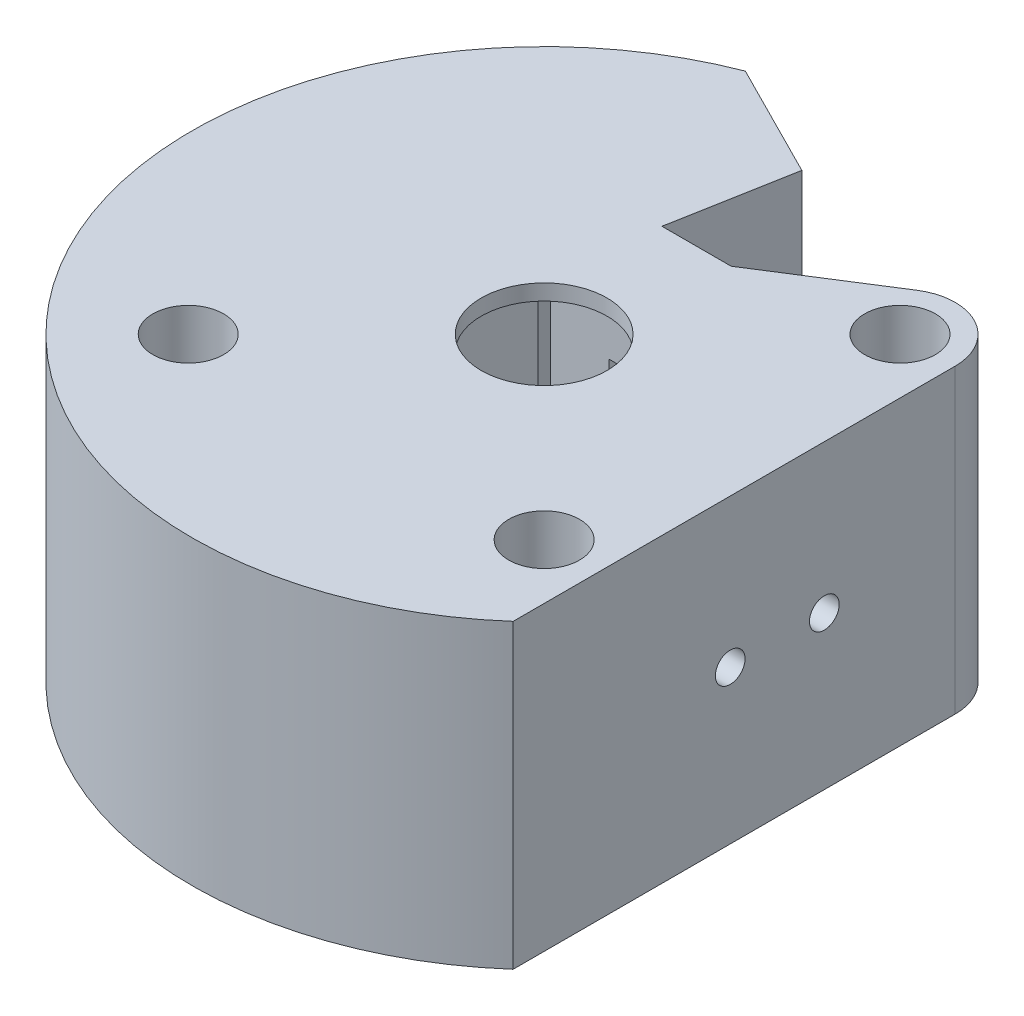
SolidWorks part; units mm, degrees
ref_plane "Front Plane" through (0, 0, 0) normal (0, 0, 1) x (1, 0, 0)
ref_plane "Top Plane" through (0, 0, 0) normal (0, 1, 0) x (1, 0, 0)
ref_plane "Right Plane" through (0, 0, 0) normal (1, 0, 0) x (0, 0, -1)
sketch "Sketch2" plane through (0, 0, 0) normal (0, 1, 0) x (1, 0, 0)
  line L0 (-46.3406, 15.0473) -> (-20.9548, -39.0545) construction
  line L1 (-17.9605, 17.9605) -> (-3.0236, 17.9605) construction
  line L2 (-17.9605, 17.9605) -> (-17.9605, -17.9605) construction
  line L3 (-17.9605, -17.9605) -> (17.9605, -17.9605) construction
  line L4 (17.9605, 17.9605) -> (17.9605, -17.9605) construction
  line L5 (-17.9605, 17.9605) -> (17.9605, -17.9605) construction
  line L6 (-17.9605, -17.9605) -> (17.9605, 17.9605) construction
  line L7 (10.05, -30.05) -> (-10.05, -30.05)
  line L8 (10.05, -30.05) -> (10.05, 10.05)
  line L9 (10.05, 10.05) -> (3.4925, 10.05)
  line L10 (-10.05, -30.05) -> (-10.05, 10.05)
  line L11 (10.05, -30.05) -> (-10.05, 10.05) construction
  line L12 (10.05, 10.05) -> (-10.05, -30.05) construction
  line L13 (-3.4925, 15.384) -> (3.4925, 15.384) construction
  line L14 (-3.4925, 15.384) -> (-3.4925, 10.05)
  line L15 (0, 10.05) -> (3.4925, 10.05) construction
  line L16 (3.4925, 15.384) -> (3.4925, 10.05)
  line L17 (0, 12.717) -> (3.4925, 10.05) construction
  line L18 (0, 12.717) -> (3.4925, 15.384) construction
  line L19 (-1.3182, 27.3309) -> (-10.8398, 32.142)
  line L20 (-1.3182, 27.3309) -> (-23.3118, -16.1961) construction
  line L21 (-23.3118, -16.1961) -> (-32.8333, -11.3851) construction
  line L22 (-10.8398, 32.142) -> (-32.8333, -11.3851) construction
  line L23 (-1.3182, 27.3309) -> (-32.8333, -11.3851) construction
  line L24 (-23.3118, -16.1961) -> (-10.8398, 32.142) construction
  line L25 (23.5324, -17.9605) -> (23.5324, -26.6597)
  line L26 (23.5324, -17.9605) -> (23.5324, 17.9605)
  line L27 (3.4925, 15.384) -> (14.9767, 22.6661)
  line L28 (-10.8398, 32.142) -> (-12.8493, 33.1573)
  line L29 (-3.4925, 15.384) -> (-1.3182, 27.3309)
  line L30 (-3.0236, 17.9605) -> (7.5558, 17.9605) construction
  line L31 (7.5558, 17.9605) -> (17.9605, 17.9605) construction
  line L32 (-3.4925, 15.384) -> (0, 12.717) construction
  line L33 (-3.4925, 10.05) -> (0, 12.717) construction
  line L34 (0, 10.05) -> (-3.4925, 10.05) construction
  line L35 (-3.4925, 10.05) -> (-10.05, 10.05)
  line L36 (-3.4925, 10.05) -> (0, 10.05) construction
  line L37 (3.4925, 10.05) -> (0, 10.05) construction
  arc A0 (-12.8493, 33.1573) -> (23.5324, -26.6597) centre (0, 0) ccw
  circle A1 centre (-17.9605, 17.9605) radius 3.5719 construction
  circle A2 centre (17.9605, 17.9605) radius 3.5719
  circle A3 centre (17.9605, -17.9605) radius 3.5719
  circle A4 centre (-17.9605, -17.9605) radius 3.5719
  arc A5 (-4.4901, 4.4901) -> (4.4901, 4.4901) centre (0, 0) ccw construction
  arc A6 (-7.1064, 7.1064) -> (7.1064, 7.1064) centre (0, 0) ccw construction
  circle A7 centre (-17.9605, -17.9605) radius 5.5719 construction
  arc A8 (23.5324, -17.9605) -> (17.9605, -12.3886) centre (17.9605, -17.9605) ccw construction
  arc A9 (23.5324, 17.9605) -> (14.9767, 22.6661) centre (17.9605, 17.9605) ccw
  arc A10 (23.5324, -26.6597) -> (-12.8493, 33.1573) centre (0, 0) ccw construction
  arc A11 (0, 10.05) -> (-7.1064, 7.1064) centre (0, 0) ccw construction
  arc A12 (4.4901, 4.4901) -> (-4.4901, 4.4901) centre (0, 0) ccw construction
  arc A13 (7.1064, 7.1064) -> (0, 10.05) centre (0, 0) ccw construction
  arc A14 (14.0206, 14.0206) -> (17.9605, 12.3886) centre (17.9605, 17.9605) ccw construction
  arc A15 (12.3886, 17.9605) -> (14.0206, 14.0206) centre (17.9605, 17.9605) ccw construction
  arc A16 (14.9767, 22.6661) -> (12.3886, 17.9605) centre (17.9605, 17.9605) ccw construction
  arc A17 (17.9605, 12.3886) -> (23.5324, 17.9605) centre (17.9605, 17.9605) ccw construction
  arc A18 (12.3886, -17.9605) -> (23.5324, -17.9605) centre (17.9605, -17.9605) ccw construction
  arc A19 (14.0206, -14.0206) -> (12.3886, -17.9605) centre (17.9605, -17.9605) ccw construction
  arc A20 (17.9605, -12.3886) -> (14.0206, -14.0206) centre (17.9605, -17.9605) ccw construction
  point P12 (0, -10)
  point P17 (0, 12.717)
  point P23 (-17.0758, 7.9729)
  point P35 (-32.1922, -15.1054)
  dimension "D1" = 71.12
  dimension "D3" = 7.1437
  dimension "D4" = 12.7
  dimension "D2" = 50.8
  dimension "D5" = 20.1
  dimension "D6" = 40.1
  dimension "D7" = 10
  dimension "D8" = 6.985
  dimension "D9" = 5.334
  dimension "D10" = 10.668
  dimension "D11" = 48.768
  dimension "D12" = 10.668
  dimension "D13" = 2
  dimension "D14" = 1
  dimension "D15" = 38.056
extrude "Boss-Extrude1" add sketch "Sketch2" along normal blind 1.905
sketch "Sketch3" plane through (0, 1.905, 0) normal (0, 1, 0) x (1, 0, 0)
  line L0 (-1.3182, 27.3309) -> (-23.3118, -16.1961) construction
  line L1 (-10.8398, 32.142) -> (-32.8333, -11.3851) construction
  line L2 (-23.3118, -16.1961) -> (-32.8333, -11.3851) construction
  line L3 (-10.8398, 32.142) -> (-32.8333, -11.3851)
  line L4 (-1.3182, 27.3309) -> (-9.7636, 10.6168)
  line L5 (-23.3118, -16.1961) -> (-32.8333, -11.3851)
  line L6 (-10.05, 10.05) -> (-9.415, 10.05) construction
  line L7 (-9.7636, 10.6168) -> (-10.05, 10.05) construction
  line L8 (-10.3364, 9.4832) -> (-23.3118, -16.1961)
  line L9 (-10.05, 10.05) -> (-10.3364, 9.4832) construction
  line L10 (-10.05, 9.415) -> (-10.05, 10.05) construction
  line L11 (-10.05, 10.05) -> (-3.4925, 10.05)
  line L12 (-3.4925, 10.05) -> (-3.4925, 15.384)
  line L13 (-3.4925, 15.384) -> (-1.3182, 27.3309)
  line L14 (-1.3182, 27.3309) -> (-12.8493, 33.1573)
  line L15 (23.5324, -26.6597) -> (23.5324, 17.9605)
  line L16 (14.9767, 22.6661) -> (3.4925, 15.384)
  line L17 (3.4925, 15.384) -> (3.4925, 10.05)
  line L18 (3.4925, 10.05) -> (10.05, 10.05)
  line L19 (10.05, 10.05) -> (10.05, -30.05)
  line L20 (10.05, -30.05) -> (-10.05, -30.05)
  line L21 (-10.05, -30.05) -> (-10.05, 10.05)
  line L22 (-9.415, 10.05) -> (-3.4925, 10.05)
  line L23 (-3.4925, 10.05) -> (-3.4925, 15.384)
  line L24 (-3.4925, 15.384) -> (-1.3182, 27.3309)
  line L25 (-10.8398, 32.142) -> (-12.8493, 33.1573)
  line L26 (23.5324, -26.6597) -> (23.5324, 17.9605)
  line L27 (14.9767, 22.6661) -> (3.4925, 15.384)
  line L28 (3.4925, 15.384) -> (3.4925, 10.05)
  line L29 (3.4925, 10.05) -> (10.05, 10.05)
  line L30 (10.05, 10.05) -> (10.05, -30.05)
  line L31 (10.05, -30.05) -> (-10.05, -30.05)
  line L32 (-10.05, -30.05) -> (-10.05, 9.415)
  line L33 (-1.3182, 27.3309) -> (-10.8398, 32.142) construction
  arc A0 (-10.3364, 9.4832) -> (-10.05, 9.415) centre (-10.05, 10.05) ccw
  circle A1 centre (17.9605, 17.9605) radius 3.5719 construction
  circle A2 centre (17.9605, -17.9605) radius 3.5719 construction
  arc A3 (-12.8493, 33.1573) -> (23.5324, -26.6597) centre (0, 0) ccw
  arc A4 (23.5324, 17.9605) -> (14.9767, 22.6661) centre (17.9605, 17.9605) ccw
  arc A5 (-12.8493, 33.1573) -> (23.5324, -26.6597) centre (0, 0) ccw
  arc A6 (23.5324, 17.9605) -> (14.9767, 22.6661) centre (17.9605, 17.9605) ccw
  circle A7 centre (-17.9605, -17.9605) radius 3.5719 construction
  circle A8 centre (17.9605, 17.9605) radius 3.5719
  circle A9 centre (17.9605, -17.9605) radius 3.5719
  circle A10 centre (-17.9605, -17.9605) radius 3.5719
  arc A11 (-9.7636, 10.6168) -> (-10.3364, 9.4832) centre (-10.05, 10.05) ccw construction
  arc A12 (-10.05, 9.415) -> (-9.415, 10.05) centre (-10.05, 10.05) ccw construction
  arc A13 (-9.415, 10.05) -> (-9.7636, 10.6168) centre (-10.05, 10.05) ccw
  dimension "D1" = 1.27
  dimension "D2" = 0
extrude "Boss-Extrude2" add sketch "Sketch3" along normal blind 19.558
sketch "Sketch4" plane through (0, 21.463, 0) normal (0, 1, 0) x (1, 0, 0)
  line L0 (0, 10.05) -> (3.4925, 10.05) construction
  line L1 (-3.4925, 15.384) -> (3.4925, 15.384) construction
  line L2 (0, 10.05) -> (-3.4925, 10.05) construction
  line L3 (0, 10.05) -> (-3.4925, 10.05)
  line L4 (0, 10.05) -> (3.4925, 10.05)
  line L5 (-3.4925, 15.384) -> (3.4925, 15.384)
  line L6 (-23.3118, -16.1961) -> (-32.8333, -11.3851) construction
  line L7 (-10.8398, 32.142) -> (-32.8333, -11.3851) construction
  line L8 (-1.3182, 27.3309) -> (-23.3118, -16.1961) construction
  line L9 (-23.3118, -16.1961) -> (-32.8333, -11.3851)
  line L10 (-10.8398, 32.142) -> (-32.8333, -11.3851)
  line L11 (-10.05, 10.05) -> (-3.4925, 10.05)
  line L12 (-10.05, -30.05) -> (-10.05, 10.05)
  line L13 (10.05, -30.05) -> (-10.05, -30.05)
  line L14 (10.05, 10.05) -> (10.05, -30.05)
  line L15 (3.4925, 10.05) -> (10.05, 10.05)
  line L16 (3.4925, 15.384) -> (3.4925, 10.05)
  line L17 (14.9767, 22.6661) -> (3.4925, 15.384)
  line L18 (23.5324, -26.6597) -> (23.5324, 17.9605)
  line L19 (-1.3182, 27.3309) -> (-12.8493, 33.1573)
  line L20 (-3.4925, 15.384) -> (-1.3182, 27.3309)
  line L21 (-3.4925, 10.05) -> (-3.4925, 15.384)
  line L22 (-9.415, 10.05) -> (-3.4925, 10.05)
  line L23 (-10.05, -30.05) -> (-10.05, 9.415)
  line L24 (10.05, -30.05) -> (-10.05, -30.05)
  line L25 (10.05, 10.05) -> (10.05, -30.05)
  line L26 (3.4925, 10.05) -> (10.05, 10.05)
  line L27 (3.4925, 15.384) -> (3.4925, 10.05) construction
  line L28 (14.9767, 22.6661) -> (3.4925, 15.384)
  line L29 (23.5324, -26.6597) -> (23.5324, 17.9605)
  line L30 (-10.8398, 32.142) -> (-12.8493, 33.1573)
  line L31 (-3.4925, 15.384) -> (-1.3182, 27.3309)
  line L32 (-3.4925, 10.05) -> (-3.4925, 15.384) construction
  line L33 (-1.3182, 27.3309) -> (-9.7636, 10.6168)
  line L34 (-1.3182, 27.3309) -> (-10.8398, 32.142) construction
  line L35 (-10.05, 10.05) -> (-10.3364, 9.4832) construction
  line L36 (-10.3364, 9.4832) -> (-23.3118, -16.1961)
  line L37 (-10.05, 9.415) -> (-10.05, 10.05) construction
  line L38 (-10.05, 10.05) -> (-9.415, 10.05) construction
  line L39 (-9.7636, 10.6168) -> (-10.05, 10.05) construction
  circle A0 centre (17.9605, 17.9605) radius 3.5719 construction
  circle A1 centre (17.9605, -17.9605) radius 3.5719 construction
  arc A2 (23.5324, 17.9605) -> (14.9767, 22.6661) centre (17.9605, 17.9605) ccw
  arc A3 (-12.8493, 33.1573) -> (23.5324, -26.6597) centre (0, 0) ccw
  arc A4 (23.5324, 17.9605) -> (14.9767, 22.6661) centre (17.9605, 17.9605) ccw
  arc A5 (-12.8493, 33.1573) -> (23.5324, -26.6597) centre (0, 0) ccw
  circle A6 centre (-17.9605, -17.9605) radius 3.5719 construction
  circle A7 centre (17.9605, 17.9605) radius 3.5719
  circle A8 centre (17.9605, -17.9605) radius 3.5719
  circle A9 centre (-17.9605, -17.9605) radius 3.5719
  arc A10 (-9.415, 10.05) -> (-9.7636, 10.6168) centre (-10.05, 10.05) ccw construction
  arc A11 (-10.3364, 9.4832) -> (-10.05, 9.415) centre (-10.05, 10.05) ccw construction
  arc A12 (-9.415, 10.05) -> (-9.7636, 10.6168) centre (-10.05, 10.05) ccw
  arc A13 (-10.3364, 9.4832) -> (-10.05, 9.415) centre (-10.05, 10.05) ccw
  dimension "D1" = 0
extrude "Boss-Extrude3" add sketch "Sketch4" along normal blind 7.366
sketch "Sketch5" plane through (0, 28.829, 0) normal (0, 1, 0) x (1, 0, 0)
  line L0 (3.4925, 15.384) -> (-3.4925, 15.384) construction
  line L1 (3.4925, 15.384) -> (-3.4925, 15.384)
  line L11 (-10.05, 10.05) -> (-3.4925, 10.05)
  line L12 (-10.05, -30.05) -> (-10.05, 10.05)
  line L13 (10.05, -30.05) -> (-10.05, -30.05)
  line L14 (10.05, 10.05) -> (10.05, -30.05)
  line L15 (3.4925, 10.05) -> (10.05, 10.05)
  line L16 (3.4925, 15.384) -> (3.4925, 10.05)
  line L17 (14.9767, 22.6661) -> (3.4925, 15.384)
  line L18 (23.5324, -26.6597) -> (23.5324, 17.9605)
  line L19 (-1.3182, 27.3309) -> (-12.8493, 33.1573)
  line L20 (-3.4925, 15.384) -> (-1.3182, 27.3309)
  line L21 (-3.4925, 10.05) -> (-3.4925, 15.384)
  line L22 (-10.05, 10.05) -> (-3.4925, 10.05) construction
  line L23 (-10.05, -30.05) -> (-10.05, 10.05) construction
  line L24 (10.05, -30.05) -> (-10.05, -30.05) construction
  line L25 (10.05, 10.05) -> (10.05, -30.05) construction
  line L26 (3.4925, 10.05) -> (10.05, 10.05) construction
  line L28 (14.9767, 22.6661) -> (3.4925, 15.384)
  line L29 (23.5324, -26.6597) -> (23.5324, 17.9605)
  line L30 (-1.3182, 27.3309) -> (-12.8493, 33.1573)
  line L31 (-3.4925, 15.384) -> (-1.3182, 27.3309)
  line L32 (-3.4925, 10.05) -> (-3.4925, 15.384) construction
  line L35 (3.4925, 15.384) -> (3.4925, 10.05) construction
  circle A0 centre (17.9605, 17.9605) radius 3.5719 construction
  circle A1 centre (17.9605, -17.9605) radius 3.5719 construction
  arc A2 (23.5324, 17.9605) -> (14.9767, 22.6661) centre (17.9605, 17.9605) ccw
  arc A3 (-12.8493, 33.1573) -> (23.5324, -26.6597) centre (0, 0) ccw
  arc A4 (23.5324, 17.9605) -> (14.9767, 22.6661) centre (17.9605, 17.9605) ccw
  arc A5 (-12.8493, 33.1573) -> (23.5324, -26.6597) centre (0, 0) ccw
  circle A6 centre (-17.9605, -17.9605) radius 3.5719 construction
  circle A7 centre (17.9605, 17.9605) radius 3.5719
  circle A8 centre (17.9605, -17.9605) radius 3.5719
  circle A9 centre (-17.9605, -17.9605) radius 3.5719
  arc A10 (4.4901, 4.4901) -> (-4.4901, 4.4901) centre (0, 0) ccw construction
  arc A11 (-4.4901, 4.4901) -> (4.4901, 4.4901) centre (0, 0) ccw construction
  arc A12 (4.4901, 4.4901) -> (-4.4901, 4.4901) centre (0, 0) ccw
  arc A13 (-4.4901, 4.4901) -> (4.4901, 4.4901) centre (0, 0) ccw
  dimension "D1" = 0
extrude "Boss-Extrude4" add sketch "Sketch5" along normal blind 1.5875
sketch "Sketch6" plane through (23.5324, 0, 0) normal (1, 0, 0) x (0, 0, -1)
  line L0 (-26.6597, 0) -> (17.9605, 0) construction
  line L1 (-4.75, 15.449) -> (4.75, 15.449) construction
  circle A0 centre (-4.75, 15.449) radius 1.5
  circle A1 centre (4.75, 15.449) radius 1.5
  point P3 (0, 15.449)
  dimension "D3" = 15.449
  dimension "D1" = 3
  dimension "D2" = 9.5
extrude "Cut-Extrude3" cut sketch "Sketch6" against normal blind 4
equation "\"AIRFRAME_OD\"= 3.091in"
equation "\"AIRFRAME_ID\"= 3.00in"
equation "\"FLAT_T\"= 0.125in"
equation "\"NOSE_EXP_L\"= 3.5in"
equation "\"NOSE_SHOULDER_L\"= 5in"
equation "\"MAIN_L\"= 30in"
equation "\"RECO_COUP_L\"= 6in"
equation "\"RECO_SWITCH_L\"= 1.5in"
equation "\"DROGUE_L\"= 14in"
equation "\"ATS_FORE_COUP_L\"= 4in"
equation "\"ATS_AFT_COUP_L\"= 2.5in"
equation "\"LOWER_L\"= 16in"
equation "\"FIN_N\"= 4"
equation "\"CR_AFT_X\"= 0.5in"
equation "\"CR_FORE_X\"= 6in"
equation "\"COUPLER_OD\"= 2.998in"
equation "\"COUPLER_ID\"= 2.875in"
equation "\"RECO_ROD_X\"= 1.5in"
equation "\"ATS_ROD_X\"= 2in"
equation "\"FIN_ROOT\"= 5in"
equation "\"FIN_X\"= 0.75in"
equation "\"MOTOR_OD\"= 2.25in"
equation "\"MOTOR_ID\"= 2.126in"
equation "\"MOTOR_L\"= 8in"
equation "\"MOTOR_LOWER_X\"= 0.5in"
equation "\"NOSE_CONE_L\"=14.5in"
equation "\"ATS_LIPO_L\"= 1.92in"
equation "\"ATS_LIPO_W\"= 0.42in"
equation "\"ATS_LIPO_H\"= 0.94in "
equation "\"ATS_STANDOFF_H\"= 10mm"
equation "\"ATS_STANDOFF_OD\"= 5.2mm"
equation "\"ATS_PCB_L\"= 2.5in"
equation "\"ATS_PCB_W\"= 1.45in"
equation "\"ATS_PCB_H\"= 1.2in"
equation "\"ATS_PCB_HOLESEP_W\"= 1.33in - 0.0985in"
equation "\"ATS_ALTI_L\"= 1.05in"
equation "\"ATS_ALTI_W\"= 0.7in"
equation "\"ATS_ALTI_H\"= 0.4in"
equation "\"D11@Sketch2\"=\"ATS_LIPO_L\""
equation "\"D12@Sketch2\"=\"ATS_LIPO_W\""
equation "\"D1@Boss-Extrude2\"=\"ATS_LIPO_H\""
